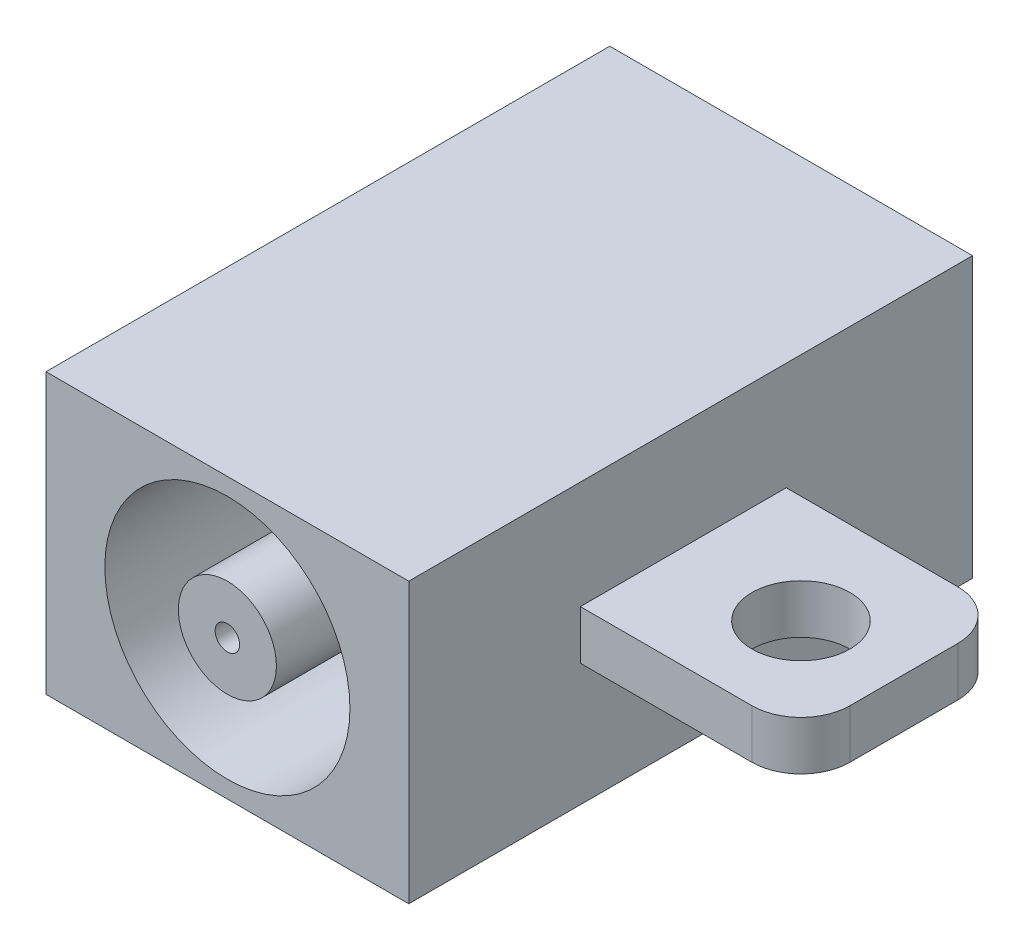
SolidWorks part; units mm, degrees
ref_plane "Front Plane" through (0, 0, 0) normal (0, 0, 1) x (1, 0, 0)
ref_plane "Top Plane" through (0, 0, 0) normal (0, 1, 0) x (1, 0, 0)
ref_plane "Right Plane" through (0, 0, 0) normal (1, 0, 0) x (0, 0, -1)
sketch "Sketch1" plane through (0, 0, 0) normal (0, 1, 0) x (1, 0, 0)
  line L1 (0, 0) -> (7.4, 0)
  line L2 (0, 0) -> (0, 11.5)
  line L3 (0, 11.5) -> (7.4, 11.5)
  line L4 (7.4, 0) -> (7.4, 11.5)
  dimension "D1" = 11.5
  dimension "D2" = 7.4
extrude "Boss-Extrude1" add sketch "Sketch1" along normal blind 5.7
sketch "Sketch2" plane through (0, 0, 0) normal (0, 0, 1) x (1, 0, 0)
  line L1 (0, 0) -> (7.4, 0) construction
  line L2 (7.4, 5.7) -> (7.4, 0) construction
  circle A0 centre (3.7, 2.85) radius 2.5
  dimension "D1" = 5
  dimension "D2" = 2.85
  dimension "D3" = 3.7
extrude "Cut-Extrude1" cut sketch "Sketch2" against normal blind 5.5
sketch "Sketch3" plane through (0, 0, 0) normal (0, 0, 1) x (1, 0, 0)
  circle A0 centre (3.7, 2.85) radius 1
  dimension "D1" = 2
extrude "Boss-Extrude2" add sketch "Sketch3" against normal blind 5.5
sketch "Sketch4" plane through (0, 0, 0) normal (0, 0, 1) x (1, 0, 0)
  circle A0 centre (3.7, 2.85) radius 0.25
  dimension "D1" = 0.5
extrude "Cut-Extrude2" cut sketch "Sketch4" against normal blind 5.5
sketch "Sketch5" plane through (7.4, 0, 0) normal (1, 0, 0) x (0, 0, -1)
  line L1 (3.5, 3.5) -> (7.7, 3.5)
  line L2 (3.5, 3.5) -> (3.5, 2.5)
  line L3 (3.5, 2.5) -> (7.7, 2.5)
  line L4 (7.7, 3.5) -> (7.7, 2.5)
  line L5 (0, 5.7) -> (0, 0) construction
  line L7 (0, 0) -> (11.5, 0) construction
  dimension "D1" = 7.7
  dimension "D2" = 1
  dimension "D3" = 4.2
  dimension "D4" = 3.5
extrude "Boss-Extrude3" add sketch "Sketch5" along normal blind 4.5
fillet "Fillet1" radius 1 2 edges at (11.9, 3, -7.7) (11.9, 3, -3.5)
sketch "Sketch6" plane through (0, 3.5, 0) normal (0, 1, 0) x (1, 0, 0)
  line L1 (10.9, 3.5) -> (7.4, 3.5) construction
  line L2 (11.9, 6.7) -> (11.9, 4.5) construction
  circle A0 centre (9.9, 5.5) radius 1
  dimension "D1" = 2
  dimension "D2" = 2
  dimension "D3" = 2
extrude "Cut-Extrude3" cut sketch "Sketch6" against normal up to next
